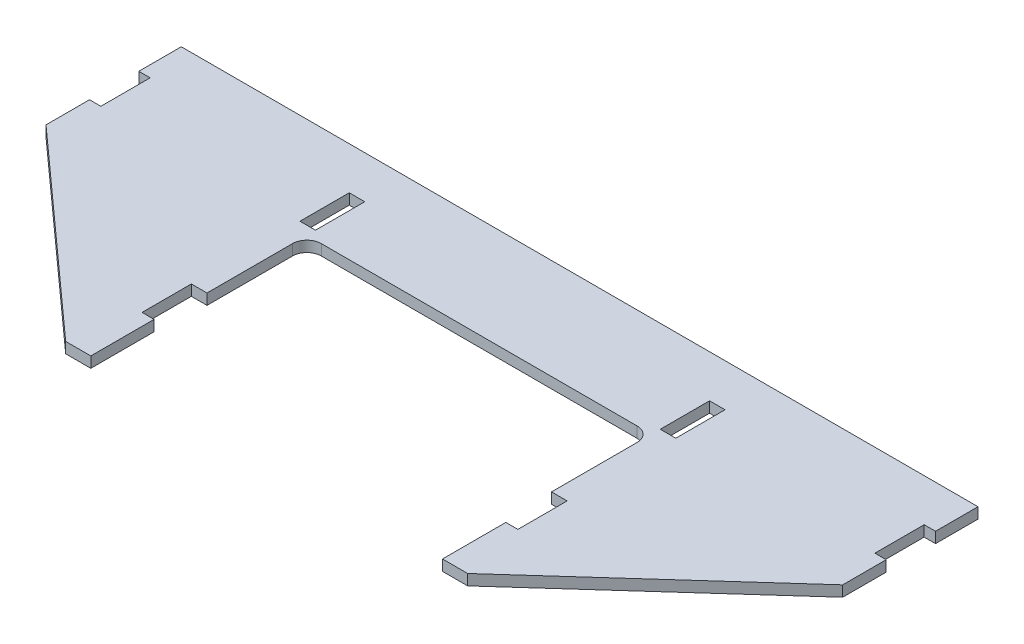
SolidWorks part; units mm, degrees
material "Plain Carbon Steel"
ref_plane "Front Plane" through (0, 0, 0) normal (0, 0, 1) x (1, 0, 0)
ref_plane "Top Plane" through (0, 0, 0) normal (0, 1, 0) x (1, 0, 0)
ref_plane "Right Plane" through (0, 0, 0) normal (1, 0, 0) x (0, 0, -1)
sketch "Sketch1" plane through (0, 0, 0) normal (0, 1, 0) x (1, 0, 0)
  line L0 (0, 29.21) -> (0, 0) construction
  line L1 (-177.8, 29.21) -> (177.8, 29.21)
  line L2 (-177.8, 29.21) -> (-177.8, -29.21)
  line L3 (-177.8, -29.21) -> (177.8, -29.21)
  line L4 (177.8, 29.21) -> (177.8, -29.21)
  line L5 (0, 0) -> (177.8, 0) construction
  dimension "D1" = 177.8
  dimension "D2" = 29.21
extrude "Boss-Extrude1" add sketch "Sketch1" along normal blind 4.7625
sketch "Sketch2" plane through (0, 4.7625, 0) normal (0, 1, 0) x (1, 0, 0)
  line L0 (177.8, -29.21) -> (88.9, -109.2458)
  line L1 (88.9, -109.2458) -> (76.2, -109.2458)
  line L2 (76.2, -109.2458) -> (76.2, -29.21)
  line L3 (-177.8, -29.21) -> (177.8, -29.21) construction
  line L4 (76.2, -29.21) -> (177.8, -29.21)
  line L5 (-177.8, -29.21) -> (-88.9, -109.2458)
  line L6 (-88.9, -109.2458) -> (-76.2, -109.2458)
  line L7 (-76.2, -109.2458) -> (-76.2, -29.21)
  line L8 (-76.2, -29.21) -> (-177.8, -29.21)
  line L9 (76.2, 29.21) -> (76.2, -109.2458) construction
  line L12 (-88.9, -109.2458) -> (-88.9, -133.0053) construction
extrude "Boss-Extrude2" add sketch "Sketch2" against normal blind 4.7625
fillet "Fillet1" radius 3.175 2 edges at (-76.2, 2.3813, 29.21)
sketch "Sketch3" plane through (0, 0, 0) normal (0, -1, 0) x (-1, 0, 0)
  line L0 (76.2, -109.2458) -> (76.2, -32.385) construction
  line L1 (82.55, -80.9889) -> (76.2, -80.9889)
  line L2 (82.55, -80.9889) -> (82.55, -59.69)
  line L3 (82.55, -59.69) -> (76.2, -59.69)
  line L4 (76.2, -80.9889) -> (76.2, -59.69)
  line L5 (177.8, 29.21) -> (177.8, -29.21) construction
  line L6 (171.45, -11.1389) -> (177.8, -11.1389)
  line L7 (171.45, -11.1389) -> (171.45, 10.16)
  line L8 (171.45, 10.16) -> (177.8, 10.16)
  line L9 (177.8, -11.1389) -> (177.8, 10.16)
  line L10 (-76.2, -32.385) -> (-76.2, -109.2458) construction
  line L11 (82.55, -11.1389) -> (76.2, -11.1389)
  line L12 (82.55, -11.1389) -> (82.55, 10.16)
  line L13 (82.55, 10.16) -> (76.2, 10.16)
  line L14 (76.2, -11.1389) -> (76.2, 10.16)
  line L15 (-82.55, 10.16) -> (-76.2, 10.16)
  line L16 (-82.55, 10.16) -> (-82.55, -11.1389)
  line L17 (-82.55, -11.1389) -> (-76.2, -11.1389)
  line L18 (-76.2, 10.16) -> (-76.2, -11.1389)
  line L19 (-82.55, -80.9889) -> (-76.2, -80.9889)
  line L20 (-82.55, -80.9889) -> (-82.55, -59.69)
  line L21 (-82.55, -59.69) -> (-76.2, -59.69)
  line L22 (-76.2, -80.9889) -> (-76.2, -59.69)
  line L23 (-177.8, -29.21) -> (-177.8, 29.21) construction
  line L24 (-171.45, -11.1389) -> (-177.8, -11.1389)
  line L25 (-171.45, -11.1389) -> (-171.45, 10.16)
  line L26 (-171.45, 10.16) -> (-177.8, 10.16)
  line L27 (-177.8, -11.1389) -> (-177.8, 10.16)
  line L28 (-171.196, -11.3929) -> (-171.196, 10.414)
  line L29 (-171.196, 10.414) -> (-178.054, 10.414)
  line L30 (-178.054, -11.3929) -> (-178.054, 10.414)
  line L31 (-171.196, -11.3929) -> (-178.054, -11.3929)
  line L32 (-75.946, 10.414) -> (-75.946, -11.3929)
  line L33 (-82.804, -11.3929) -> (-75.946, -11.3929)
  line L34 (-82.804, 10.414) -> (-82.804, -11.3929)
  line L35 (-82.804, 10.414) -> (-75.946, 10.414)
  line L36 (-75.946, -81.2429) -> (-75.946, -59.436)
  line L37 (-82.804, -59.436) -> (-75.946, -59.436)
  line L38 (-82.804, -81.2429) -> (-82.804, -59.436)
  line L39 (-82.804, -81.2429) -> (-75.946, -81.2429)
  line L40 (82.804, -81.2429) -> (82.804, -59.436)
  line L41 (82.804, -59.436) -> (75.946, -59.436)
  line L42 (75.946, -81.2429) -> (75.946, -59.436)
  line L43 (82.804, -81.2429) -> (75.946, -81.2429)
  line L44 (82.804, -11.3929) -> (82.804, 10.414)
  line L45 (82.804, 10.414) -> (75.946, 10.414)
  line L46 (75.946, -11.3929) -> (75.946, 10.414)
  line L47 (82.804, -11.3929) -> (75.946, -11.3929)
  line L48 (171.196, -11.3929) -> (171.196, 10.414)
  line L49 (171.196, 10.414) -> (178.054, 10.414)
  line L50 (178.054, -11.3929) -> (178.054, 10.414)
  line L51 (171.196, -11.3929) -> (178.054, -11.3929)
  dimension "D1" = 0.254
extrude "Cut-Extrude1" cut sketch "Sketch3" against normal through all
sketch "Sketch4" plane through (0, 4.7625, 0) normal (0, 1, 0) x (1, 0, 0)
  line L0 (176.2125, 29.21) -> (176.2125, -30.6392)
  line L1 (177.8, 29.21) -> (-177.8, 29.21) construction
  line L2 (88.9, -109.2458) -> (177.8, -29.21) construction
  line L3 (-176.2125, 29.21) -> (-176.2125, -30.6392)
  line L4 (-177.8, -29.21) -> (-88.9, -109.2458) construction
  line L31 (-171.196, -11.3929) -> (-177.8, -11.3929)
  line L32 (-177.8, -11.3929) -> (-177.8, -29.21)
  line L33 (-177.8, -29.21) -> (-88.9, -109.2458)
  line L34 (-88.9, -109.2458) -> (-76.2, -109.2458)
  line L35 (-76.2, -109.2458) -> (-76.2, -81.2429)
  line L36 (-76.2, -81.2429) -> (-82.804, -81.2429)
  line L37 (-82.804, -81.2429) -> (-82.804, -59.436)
  line L38 (-82.804, -59.436) -> (-76.2, -59.436)
  line L39 (-76.2, -59.436) -> (-76.2, -32.385)
  line L40 (-73.025, -29.21) -> (73.025, -29.21)
  line L41 (76.2, -32.385) -> (76.2, -59.436)
  line L42 (76.2, -59.436) -> (82.804, -59.436)
  line L43 (82.804, -59.436) -> (82.804, -81.2429)
  line L44 (82.804, -81.2429) -> (76.2, -81.2429)
  line L45 (76.2, -81.2429) -> (76.2, -109.2458)
  line L46 (76.2, -109.2458) -> (88.9, -109.2458)
  line L47 (88.9, -109.2458) -> (177.8, -29.21)
  line L48 (177.8, -29.21) -> (177.8, -11.3929)
  line L49 (177.8, -11.3929) -> (171.196, -11.3929)
  line L50 (171.196, -11.3929) -> (171.196, 10.414)
  line L51 (171.196, 10.414) -> (177.8, 10.414)
  line L52 (177.8, 10.414) -> (177.8, 29.21)
  line L53 (177.8, 29.21) -> (-177.8, 29.21)
  line L54 (-177.8, 29.21) -> (-177.8, 10.414)
  line L55 (-177.8, 10.414) -> (-171.196, 10.414)
  line L56 (-171.196, 10.414) -> (-171.196, -11.3929)
  line L57 (-171.196, -11.3929) -> (-177.8, -11.3929)
  line L58 (-177.8, -11.3929) -> (-177.8, -29.21)
  line L59 (-177.8, -29.21) -> (-88.9, -109.2458)
  line L60 (-88.9, -109.2458) -> (-76.2, -109.2458)
  line L61 (-76.2, -109.2458) -> (-76.2, -81.2429)
  line L62 (-76.2, -81.2429) -> (-82.804, -81.2429)
  line L63 (-82.804, -81.2429) -> (-82.804, -59.436)
  line L64 (-82.804, -59.436) -> (-76.2, -59.436)
  line L65 (-76.2, -59.436) -> (-76.2, -32.385)
  line L66 (-73.025, -29.21) -> (73.025, -29.21)
  line L67 (76.2, -32.385) -> (76.2, -59.436)
  line L68 (76.2, -59.436) -> (82.804, -59.436)
  line L69 (82.804, -59.436) -> (82.804, -81.2429)
  line L70 (82.804, -81.2429) -> (76.2, -81.2429)
  line L71 (76.2, -81.2429) -> (76.2, -109.2458)
  line L72 (76.2, -109.2458) -> (88.9, -109.2458)
  line L73 (88.9, -109.2458) -> (177.8, -29.21)
  line L74 (177.8, -29.21) -> (177.8, -11.3929)
  line L75 (177.8, -11.3929) -> (171.196, -11.3929)
  line L76 (171.196, -11.3929) -> (171.196, 10.414)
  line L77 (171.196, 10.414) -> (177.8, 10.414)
  line L78 (177.8, 10.414) -> (177.8, 29.21)
  line L79 (177.8, 29.21) -> (-177.8, 29.21)
  line L80 (-177.8, 29.21) -> (-177.8, 10.414)
  line L81 (-177.8, 10.414) -> (-171.196, 10.414)
  line L82 (-171.196, 10.414) -> (-171.196, -11.3929)
  arc A2 (-73.025, -29.21) -> (-76.2, -32.385) centre (-73.025, -32.385) ccw
  arc A3 (-73.025, -29.21) -> (-76.2, -32.385) centre (-73.025, -32.385) ccw
  arc A4 (76.2, -32.385) -> (73.025, -29.21) centre (73.025, -32.385) ccw
  arc A5 (76.2, -32.385) -> (73.025, -29.21) centre (73.025, -32.385) ccw
  line M29 (-171.196, -11.3929) -> (-177.8, -11.3929)
  line M30 (-177.8, -11.3929) -> (-177.8, -29.21)
  line M31 (-177.8, -29.21) -> (-88.9, -109.2458)
  line M47 (88.9, -109.2458) -> (177.8, -29.21)
  line M48 (177.8, -29.21) -> (177.8, -11.3929)
  line M49 (177.8, -11.3929) -> (171.196, -11.3929)
  line M51 (171.196, 10.414) -> (177.8, 10.414)
  line M52 (177.8, 10.414) -> (177.8, 29.21)
  line M53 (177.8, 29.21) -> (-177.8, 29.21)
  line M54 (-177.8, 29.21) -> (-177.8, 10.414)
  line M55 (-177.8, 10.414) -> (-171.196, 10.414)
  dimension "D1" = 0
  dimension "D2" = 1.5875
  dimension "D3" = 1.5875
extrude "Cut-Extrude2" cut sketch "Sketch4" against normal through all contours L0 M49 M47 M48 | L0 M53 M51 M52 | L3 M53 M54 M55 | L3 M29 M30 M31
sketch "Sketch5" plane through (0, 4.7625, 0) normal (0, 1, 0) x (1, 0, 0)
  line L0 (-77.7875, -59.436) -> (-77.7875, -32.385)
  line L1 (-73.025, -27.6225) -> (73.025, -27.6225)
  line L2 (77.7875, -32.385) -> (77.7875, -59.436)
  line L3 (-77.7875, -59.436) -> (-77.7875, -109.2458)
  line L4 (77.7875, -59.436) -> (77.7875, -109.2458)
  line L26 (-171.196, -11.3929) -> (-176.2125, -11.3929)
  line L27 (-176.2125, -11.3929) -> (-176.2125, -30.6392)
  line L28 (-176.2125, -30.6392) -> (-88.9, -109.2458)
  line L29 (-88.9, -109.2458) -> (-76.2, -109.2458)
  line L30 (-76.2, -109.2458) -> (-76.2, -81.2429)
  line L31 (-76.2, -81.2429) -> (-82.804, -81.2429)
  line L32 (-82.804, -81.2429) -> (-82.804, -59.436)
  line L33 (-82.804, -59.436) -> (-76.2, -59.436)
  line L34 (-76.2, -59.436) -> (-76.2, -32.385)
  line L35 (-73.025, -29.21) -> (73.025, -29.21)
  line L36 (76.2, -32.385) -> (76.2, -59.436)
  line L37 (76.2, -59.436) -> (82.804, -59.436)
  line L38 (82.804, -59.436) -> (82.804, -81.2429)
  line L39 (82.804, -81.2429) -> (76.2, -81.2429)
  line L40 (76.2, -81.2429) -> (76.2, -109.2458)
  line L41 (76.2, -109.2458) -> (88.9, -109.2458)
  line L42 (88.9, -109.2458) -> (176.2125, -30.6392)
  line L43 (176.2125, -30.6392) -> (176.2125, -11.3929)
  line L44 (176.2125, -11.3929) -> (171.196, -11.3929)
  line L45 (171.196, -11.3929) -> (171.196, 10.414)
  line L46 (171.196, 10.414) -> (176.2125, 10.414)
  line L47 (176.2125, 10.414) -> (176.2125, 29.21)
  line L48 (176.2125, 29.21) -> (-176.2125, 29.21)
  line L49 (-176.2125, 29.21) -> (-176.2125, 10.414)
  line L50 (-176.2125, 10.414) -> (-171.196, 10.414)
  line L51 (-171.196, 10.414) -> (-171.196, -11.3929)
  line L52 (-171.196, -11.3929) -> (-176.2125, -11.3929)
  line L53 (-176.2125, -11.3929) -> (-176.2125, -30.6392)
  line L54 (-176.2125, -30.6392) -> (-88.9, -109.2458)
  line L55 (-88.9, -109.2458) -> (-76.2, -109.2458)
  line L56 (-76.2, -109.2458) -> (-76.2, -81.2429)
  line L57 (-76.2, -81.2429) -> (-82.804, -81.2429)
  line L58 (-82.804, -81.2429) -> (-82.804, -59.436)
  line L59 (-82.804, -59.436) -> (-76.2, -59.436)
  line L60 (-76.2, -59.436) -> (-76.2, -32.385)
  line L61 (-73.025, -29.21) -> (73.025, -29.21)
  line L62 (76.2, -32.385) -> (76.2, -59.436)
  line L63 (76.2, -59.436) -> (82.804, -59.436)
  line L64 (82.804, -59.436) -> (82.804, -81.2429)
  line L65 (82.804, -81.2429) -> (76.2, -81.2429)
  line L66 (76.2, -81.2429) -> (76.2, -109.2458)
  line L67 (76.2, -109.2458) -> (88.9, -109.2458)
  line L68 (88.9, -109.2458) -> (176.2125, -30.6392)
  line L69 (176.2125, -30.6392) -> (176.2125, -11.3929)
  line L70 (176.2125, -11.3929) -> (171.196, -11.3929)
  line L71 (171.196, -11.3929) -> (171.196, 10.414)
  line L72 (171.196, 10.414) -> (176.2125, 10.414)
  line L73 (176.2125, 10.414) -> (176.2125, 29.21)
  line L74 (176.2125, 29.21) -> (-176.2125, 29.21)
  line L75 (-176.2125, 29.21) -> (-176.2125, 10.414)
  line L76 (-176.2125, 10.414) -> (-171.196, 10.414)
  line L77 (-171.196, 10.414) -> (-171.196, -11.3929)
  arc A0 (-73.025, -27.6225) -> (-77.7875, -32.385) centre (-73.025, -32.385) ccw
  arc A1 (77.7875, -32.385) -> (73.025, -27.6225) centre (73.025, -32.385) ccw
  arc A4 (-73.025, -29.21) -> (-76.2, -32.385) centre (-73.025, -32.385) ccw
  arc A5 (-73.025, -29.21) -> (-76.2, -32.385) centre (-73.025, -32.385) ccw
  arc A6 (-73.025, -29.21) -> (-76.2, -32.385) centre (-73.025, -32.385) ccw construction
  arc A7 (76.2, -32.385) -> (73.025, -29.21) centre (73.025, -32.385) ccw construction
  arc A8 (76.2, -32.385) -> (73.025, -29.21) centre (73.025, -32.385) ccw
  arc A9 (76.2, -32.385) -> (73.025, -29.21) centre (73.025, -32.385) ccw
  line M40 (-88.9, -109.2458) -> (-76.2, -109.2458)
  line M41 (-76.2, -109.2458) -> (-76.2, -81.2429)
  line M42 (-76.2, -81.2429) -> (-82.804, -81.2429)
  line M52 (82.804, -81.2429) -> (76.2, -81.2429)
  line M53 (76.2, -81.2429) -> (76.2, -109.2458)
  line M54 (76.2, -109.2458) -> (88.9, -109.2458)
  dimension "D1" = 0
  dimension "D2" = 1.5875
extrude "Cut-Extrude3" cut sketch "Sketch5" against normal through all contours L3 M42 M40 M41 | L4 M52 M53 M54
sketch "Sketch6" plane through (0, 0, 0) normal (0, -1, 0) x (1, 0, 0)
  line L0 (-82.804, -10.414) -> (-75.946, -10.414) construction
  line L1 (-75.946, 11.3929) -> (-76.2635, 11.3929)
  line L2 (-75.946, 11.3929) -> (-75.946, -10.414)
  line L3 (-75.946, -10.414) -> (-76.2635, -10.414)
  line L4 (-76.2635, 11.3929) -> (-76.2635, -10.414)
  line L5 (75.946, -10.414) -> (82.804, -10.414) construction
  line L6 (75.946, 11.3929) -> (76.2635, 11.3929)
  line L7 (75.946, 11.3929) -> (75.946, -10.414)
  line L8 (75.946, -10.414) -> (76.2635, -10.414)
  line L9 (76.2635, 11.3929) -> (76.2635, -10.414)
  dimension "D1" = 152.527
extrude "Boss-Extrude3" add sketch "Sketch6" against normal up to surface (4.7625 mm away) up to face at (79.375, 4.7625, 0.4895)
sketch "Sketch7" plane through (0, 0, 0) normal (0, -1, 0) x (1, 0, 0)
  line L0 (-82.804, 59.436) -> (-76.2, 59.436) construction
  line L1 (-82.804, 11.3929) -> (-83.1215, 11.3929)
  line L2 (-82.804, 11.3929) -> (-82.804, -10.414)
  line L3 (-82.804, -10.414) -> (-83.1215, -10.414)
  line L4 (-83.1215, 11.3929) -> (-83.1215, -10.414)
  line L5 (-82.804, 81.2429) -> (-83.1215, 81.2429)
  line L6 (-82.804, 81.2429) -> (-82.804, 59.436)
  line L7 (-82.804, 59.436) -> (-83.1215, 59.436)
  line L8 (-83.1215, 81.2429) -> (-83.1215, 59.436)
  line L9 (82.804, 81.2429) -> (83.1215, 81.2429)
  line L10 (82.804, 81.2429) -> (82.804, 59.436)
  line L11 (82.804, 59.436) -> (83.1215, 59.436)
  line L12 (83.1215, 81.2429) -> (83.1215, 59.436)
  line L13 (82.804, 11.3929) -> (83.1215, 11.3929)
  line L14 (82.804, 11.3929) -> (82.804, -10.414)
  line L15 (82.804, -10.414) -> (83.1215, -10.414)
  line L16 (83.1215, 11.3929) -> (83.1215, -10.414)
  line L17 (-82.804, -10.414) -> (-76.2635, -10.414) construction
  line L18 (76.2635, -10.414) -> (76.2635, 11.3929) construction
  dimension "D1" = 6.858
extrude "Cut-Extrude4" cut sketch "Sketch7" against normal through all
sketch "Sketch8" plane through (0, 4.7625, 0) normal (0, 1, 0) x (1, 0, 0)
  line L0 (176.2125, 29.21) -> (-176.2125, 29.21) construction
  line L1 (-76.2, -32.385) -> (76.2, -32.385)
  line L2 (-76.2, -32.385) -> (-76.2, -15.24)
  line L3 (-76.2, -15.24) -> (76.2, -15.24)
  line L4 (76.2, -32.385) -> (76.2, -15.24)
  dimension "D1" = 44.45
extrude "Cut-Extrude5" cut sketch "Sketch8" against normal through all
fillet "Fillet2" radius 6.35 2 edges at (76.2, 2.3813, 15.24) (-76.2, 2.3813, 15.24)
